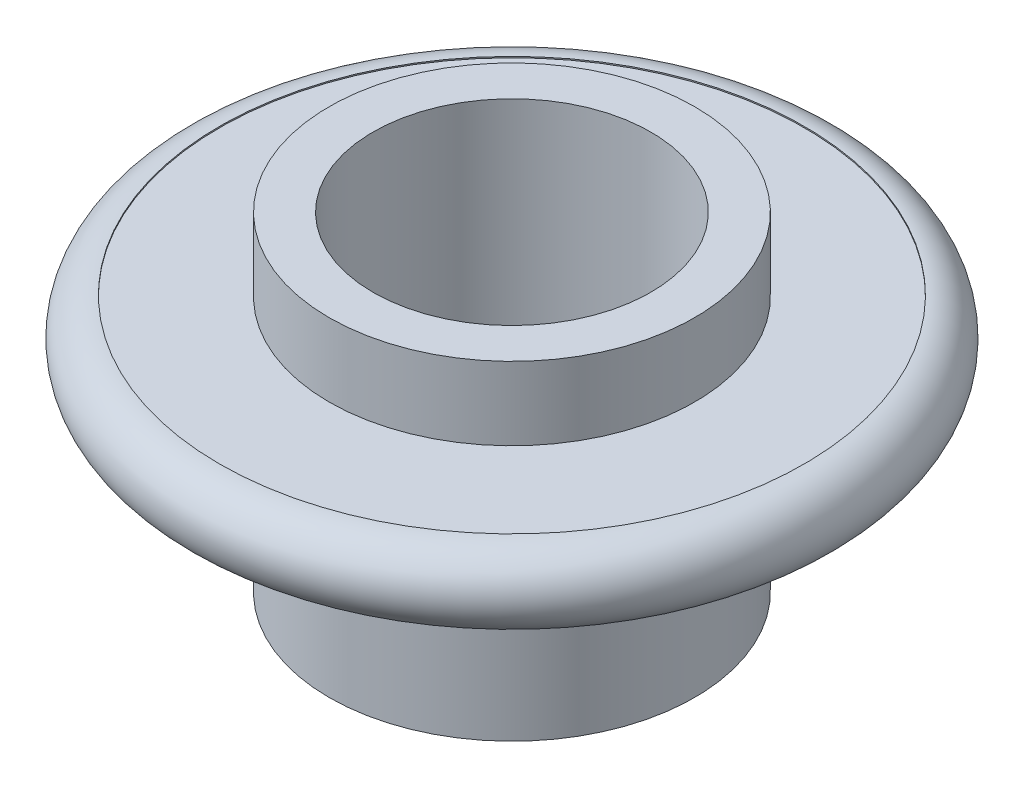
SolidWorks part; units mm, degrees
ref_plane "Front Plane" through (0, 0, 0) normal (0, 0, 1) x (1, 0, 0)
ref_plane "Top Plane" through (0, 0, 0) normal (0, 1, 0) x (1, 0, 0)
ref_plane "Right Plane" through (0, 0, 0) normal (1, 0, 0) x (0, 0, -1)
sketch "Sketch1" plane through (0, 0, 0) normal (0, 0, 1) x (1, 0, 0)
  line L0 (0, 56.7978) -> (0, -48.6224) construction
  line L1 (19, 34.1895) -> (19, -10.8105)
  line L2 (19, -10.8105) -> (25, -10.8105)
  line L3 (25, -10.8105) -> (25, 14.1895)
  line L4 (25, 14.1895) -> (40, 14.1895)
  line L5 (19, 34.1895) -> (25, 34.1895)
  line L6 (25, 34.1895) -> (25, 24.1895)
  line L7 (25, 24.1895) -> (40, 24.1895)
  line L8 (40, 24.1895) -> (40, 24.359)
  arc A0 (40, 14.1895) -> (40, 24.359) centre (40, 19.2742) ccw
  dimension "D1" = 10
  dimension "D2" = 10
  dimension "D3" = 45
  dimension "D4" = 19
  dimension "D5" = 25
  dimension "D6" = 25
  dimension "D7" = 40
revolve "Revolve1" add sketch "Sketch1" angle 360 about L0
